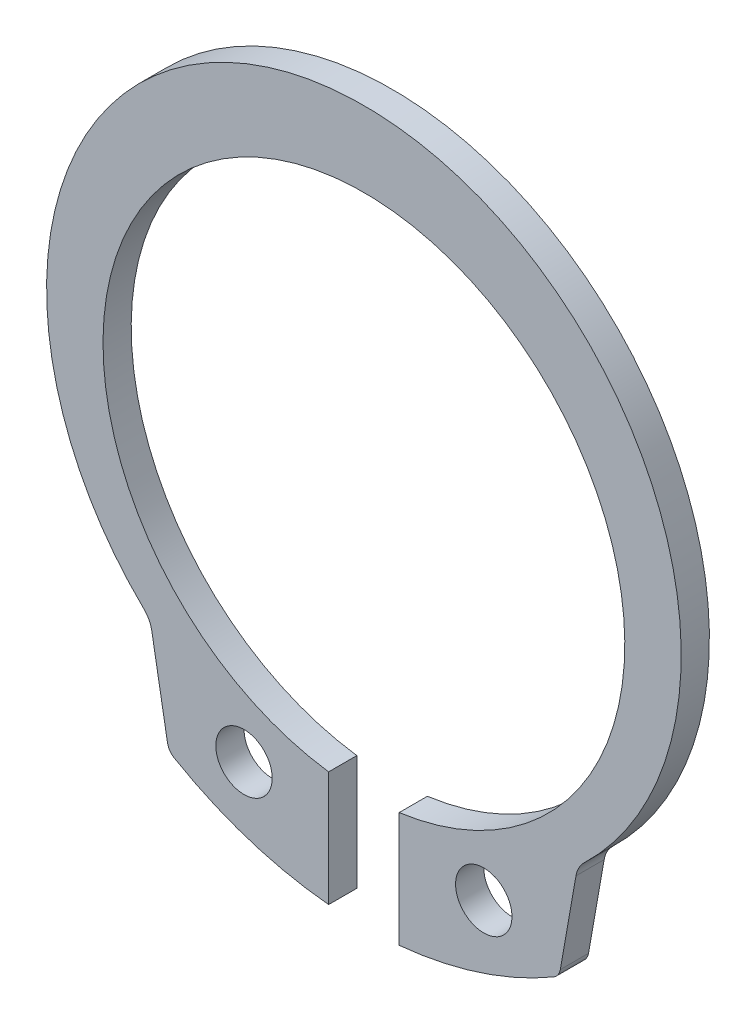
SolidWorks part; units mm, degrees
ref_plane "Front" through (0, 0, 0) normal (0, 0, 1) x (1, 0, 0)
ref_plane "Top" through (0, 0, 0) normal (0, 1, 0) x (1, 0, 0)
ref_plane "Right" through (0, 0, 0) normal (1, 0, 0) x (0, 0, -1)
sketch "Sketch1" plane through (0, 0, 0) normal (0, 0, 1) x (1, 0, 0)
  line L0 (0, 4.2365) -> (0, -4.9012) construction
  line L1 (-1.25, -9.8352) -> (-1.25, -13.9111)
  line L2 (1.25, -9.8352) -> (1.25, -13.9111)
  line L3 (11.2, -0.67) -> (-11.2, -0.67) construction
  line L4 (7.5771, -8.3156) -> (6.9229, -12.0262)
  line L7 (-7.5771, -8.3156) -> (-6.9229, -12.0262)
  line L8 (-7.5771, -8.3156) -> (-7.5771, -16.3863) construction
  arc A0 (1.25, -9.8352) -> (-1.25, -9.8352) centre (0, -0.67) ccw
  arc A1 (7.5771, -8.3156) -> (-7.5771, -8.3156) centre (0, 0) ccw
  arc A2 (-11.2, -0.67) -> (11.2, -0.67) centre (0, -0.67) ccw construction
  arc A3 (6.9229, -12.0262) -> (1.25, -13.9111) centre (0, -0.67) cw
  arc A4 (-6.9229, -12.0262) -> (-1.25, -13.9111) centre (0, -0.67) ccw
  circle A5 centre (4.25, -11.0323) radius 1
  circle A6 centre (-4.25, -11.0323) radius 1
  point P17 (-7.25, -10.1709)
  dimension "d" = 18.5
  dimension "D2" = 10
  dimension "d0" = 22.5
  dimension "d1" = 2
  dimension "R1" = 11.2
  dimension "R" = 13.3
  dimension "B1" = 2.5
  dimension "C" = 0.67
  dimension "L" = 14.5
  dimension "B2" = 8.5
extrude "Body" add sketch "Sketch1" against normal blind 1
fillet "Fillet1" radius 0.5 2 edges at (-6.9229, -12.0262, -0.5) (6.9229, -12.0262, -0.5)
fillet "Fillet2" radius 1 2 edges at (7.5771, -8.3156, -0.5) (-7.5771, -8.3156, -0.5)
